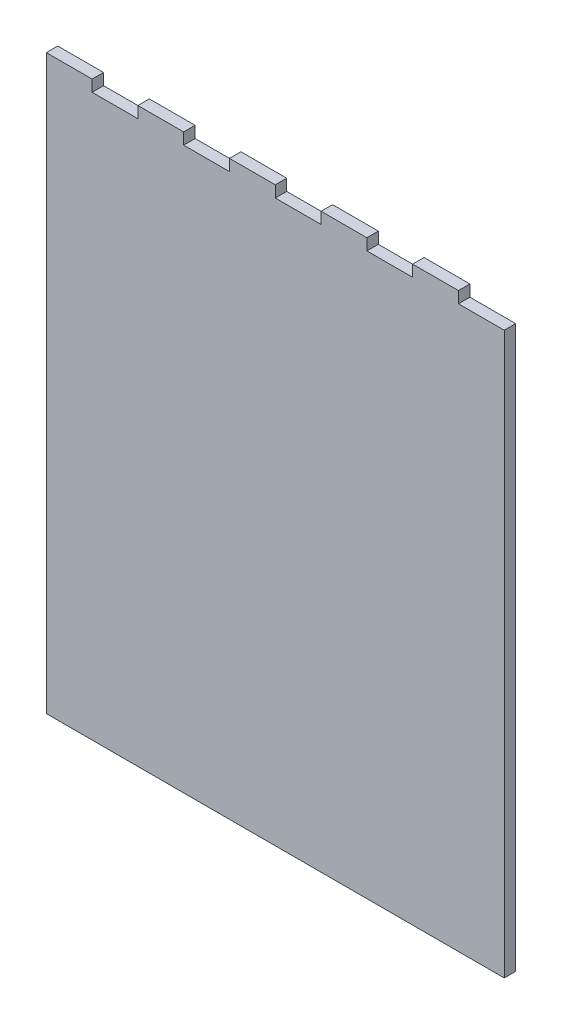
SolidWorks part; units mm, degrees
ref_plane "Front Plane" through (0, 0, 0) normal (0, 0, 1) x (1, 0, 0)
ref_plane "Top Plane" through (0, 0, 0) normal (0, 1, 0) x (1, 0, 0)
ref_plane "Right Plane" through (0, 0, 0) normal (1, 0, 0) x (0, 0, -1)
sketch "Sketch1" plane through (0, 0, 0) normal (0, 0, 1) x (1, 0, 0)
  line L1 (0, 0) -> (254, 0)
  line L2 (0, 0) -> (0, 317.5)
  line L3 (0, 317.5) -> (254, 317.5)
  line L4 (254, 0) -> (254, 317.5)
  dimension "D1" = 317.5
  dimension "D2" = 254
extrude "Boss-Extrude1" add sketch "Sketch1" along normal blind 6.35
sketch "Sketch2" plane through (0, 0, 0) normal (0, 0, 1) x (1, 0, 0)
  line L0 (254, 317.5) -> (0, 317.5) construction
  line L1 (25.4, 317.5) -> (50.8, 317.5)
  line L2 (25.4, 317.5) -> (25.4, 311.15)
  line L3 (25.4, 311.15) -> (50.8, 311.15)
  line L4 (50.8, 317.5) -> (50.8, 311.15)
  line L5 (0, 317.5) -> (0, 0) construction
  dimension "D1" = 6.35
  dimension "D2" = 25.4
  dimension "D3" = 25.4
extrude "Cut-Extrude1" cut sketch "Sketch2" along normal blind 6.35
pattern_linear "LPattern1" count 5 spacing 50.8 along (1, 0, 0) of "Cut-Extrude1"
